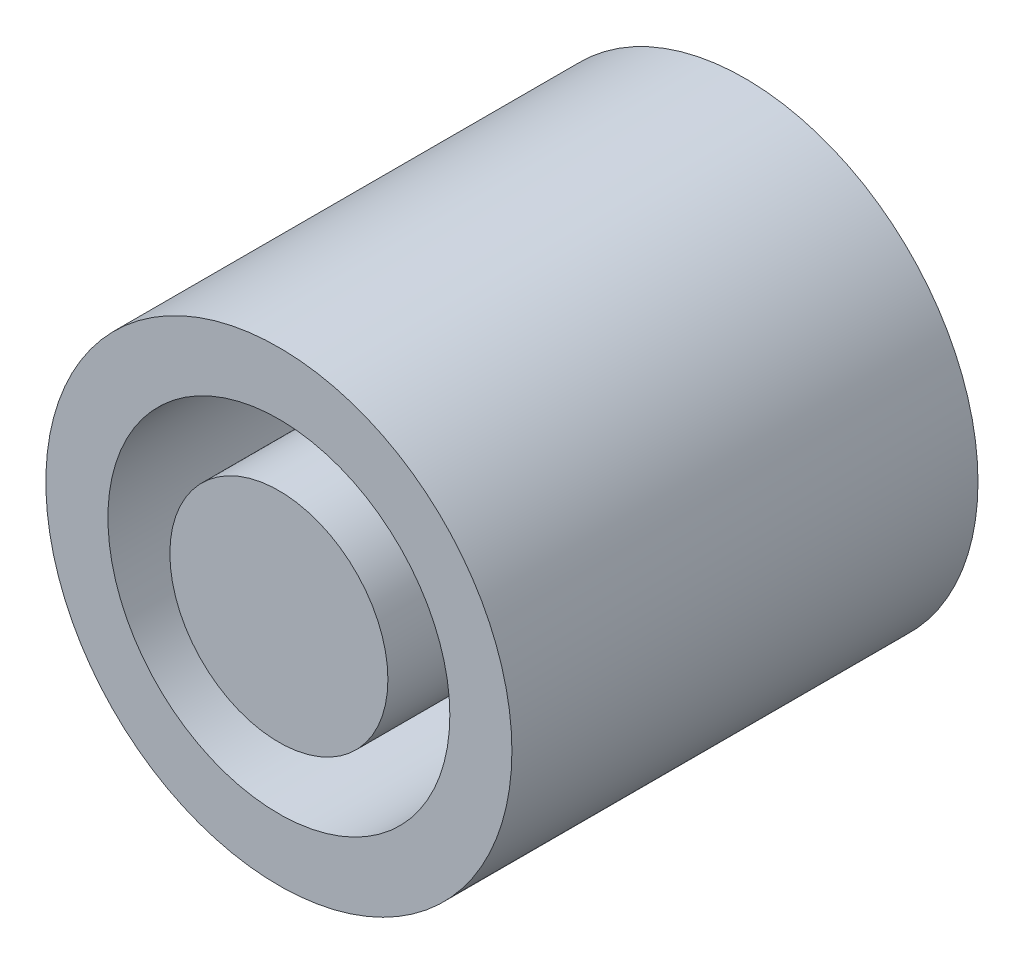
SolidWorks part; units mm, degrees
ref_plane "Front Plane" through (0, 0, 0) normal (0, 0, 1) x (1, 0, 0)
ref_plane "Top Plane" through (0, 0, 0) normal (0, 1, 0) x (1, 0, 0)
ref_plane "Right Plane" through (0, 0, 0) normal (1, 0, 0) x (0, 0, -1)
sketch "Sketch1" plane through (0, 0, 0) normal (0, 0, 1) x (1, 0, 0)
  circle A0 centre (0, 0) radius 0.025
  dimension "D1" = 0.05
extrude "Extrude1" add sketch "Sketch1" against normal blind 0.05
sketch "Sketch2" plane through (0, 0, 0) normal (0, 0, 1) x (1, 0, 0)
  circle A0 centre (0, 0) radius 0.0117
  circle A1 centre (0, 0) radius 0.0183
extrude "Extrude2" cut sketch "Sketch2" against normal blind 0.04
